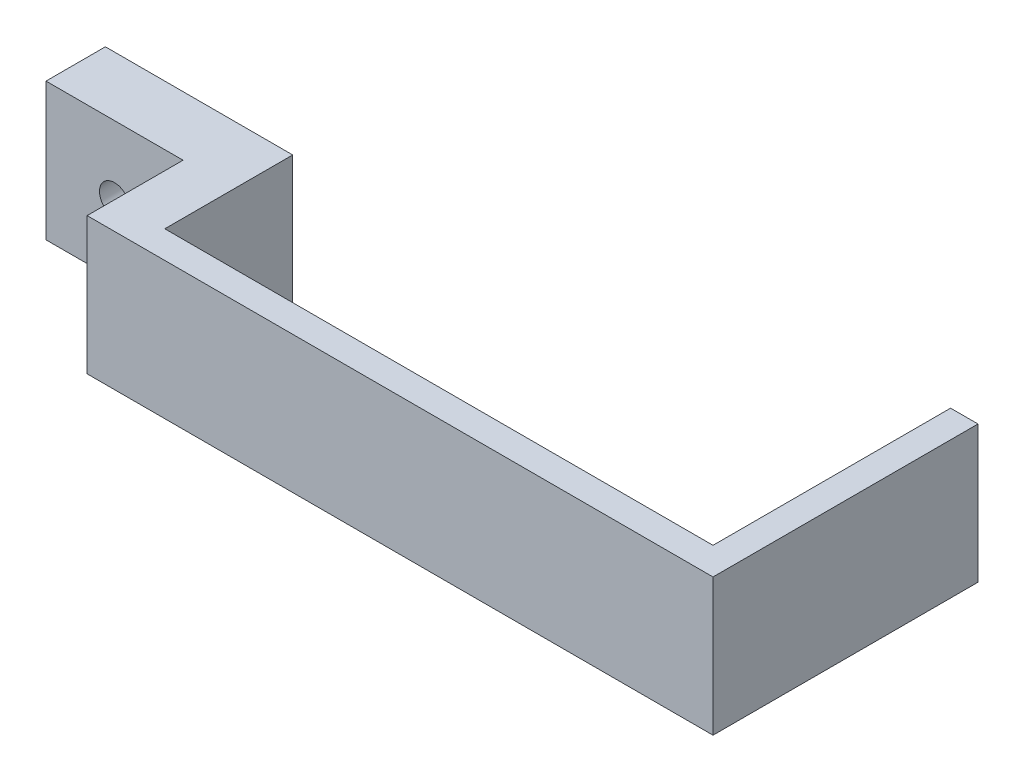
SolidWorks part; units mm, degrees
ref_plane "Front Plane" through (0, 0, 0) normal (0, 0, 1) x (1, 0, 0)
ref_plane "Top Plane" through (0, 0, 0) normal (0, 1, 0) x (1, 0, 0)
ref_plane "Right Plane" through (0, 0, 0) normal (1, 0, 0) x (0, 0, -1)
sketch "Esboço1" plane through (0, 0, 0) normal (0, 0, 1) x (1, 0, 0)
  line L0 (59.5, -104.7634) -> (59.5, -76.9) construction
  line L1 (59.5, -82.5) -> (-70.5, -82.5)
  line L3 (59.5, -52.5) -> (-70.5, -52.5)
  line L4 (-70.5, -82.5) -> (-70.5, -52.5)
  line L5 (-70.5, -286.2233) -> (-70.5, 153.7767) construction
  line L7 (-56.7634, -107.5) -> (56.7634, -107.5) construction
  line L16 (59.5, -52.5) -> (66.5, -52.5)
  line L18 (59.5, -82.5) -> (66.5, -82.5)
  line L19 (66.5, -52.5) -> (66.5, -82.5)
  dimension "D1" = 30
  dimension "D2" = 7
  dimension "D3" = 25
extrude "Ressalto-extrusão1" add sketch "Esboço1" along normal blind 6
sketch "Esboço2" plane through (0, 0, 0) normal (0, 0, -1) x (-1, 0, 0)
  line L1 (70.5, -52.5) -> (59.5, -52.5)
  line L2 (70.5, -52.5) -> (70.5, -82.6)
  line L3 (70.5, -82.6) -> (59.5, -82.6)
  line L4 (59.5, -52.5) -> (59.5, -82.6)
extrude "Ressalto-extrusão2" add sketch "Esboço2" along normal blind 28
sketch "Esboço3" plane through (-70.5, 0, 0) normal (-1, 0, 0) x (0, 0, 1)
  line L0 (-15, -286.2233) -> (-15, 153.7767) construction
  line L1 (-28, -52.5) -> (-15, -52.5)
  line L2 (-28, -52.5) -> (-28, -82.6)
  line L3 (-28, -82.6) -> (-15, -82.6)
  line L4 (-15, -52.5) -> (-15, -82.6)
  line L5 (-28, -82.6) -> (0, -82.6) construction
extrude "Ressalto-extrusão3" add sketch "Esboço3" along normal up to vertex (30 mm away)
sketch "Esboço5" plane through (0, 0, -28) normal (0, 0, -1) x (-1, 0, 0)
  line L0 (100.5, -67.55) -> (73.0736, -67.55) construction
  line L1 (100.5, -52.5) -> (100.5, -82.6) construction
  line L2 (85.5, -226.2233) -> (85.5, -11.4726) construction
  line L3 (100.5, -226.2233) -> (70.5, -226.2233) construction
hole_wizard "Rebaixo para parafuso de máquina com cabeça panela de M61" positions "3DSketch1" profile "Esboço6" counterbore size "M6" standard "Ansi Metric" end condition through all
sketch3d "3DSketch1"
  line L0 (-100.5, -67.55, -28) -> (-73.0736, -67.55, -28) construction
  point P0 (-85.4929, -67.55, -28)
sketch "Esboço6" plane through (-85.4929, -67.55, -28) normal (1, 0, 0) x (0, 1, 0)
  line L0 (0, 0) -> (0, 34)
  line L1 (0, 34) -> (3.3, 34)
  line L3 (3.3, 34) -> (3.3, 4.6)
  line L4 (3.3, 4.6) -> (6.5, 4.6)
  line L5 (6.5, 4.6) -> (6.5, 0)
  line L7 (6.5, 0) -> (0, 0)
  line L11 (0, -6.35) -> (0, 107.95) construction
  dimension "Thru Hole Dia." = 6.6
  dimension "Thru Hole Depth" = 34
  dimension "C'Bore Dia." = 13
  dimension "C'Bore Depth" = 4.6
sketch "Esboço7" plane through (0, 0, 0) normal (0, 0, -1) x (-1, 0, 0)
  line L0 (59.5, -82.5) -> (-66.5, -82.5) construction
  line L1 (-66.5, -52.5) -> (-60.5, -52.5)
  line L2 (-66.5, -52.5) -> (-66.5, -82.5)
  line L3 (-66.5, -82.5) -> (-60.5, -82.5)
  line L4 (-60.5, -52.5) -> (-60.5, -82.5)
  dimension "D1" = 6
extrude "Ressalto-extrusão4" add sketch "Esboço7" along normal up to vertex (52 mm away)
